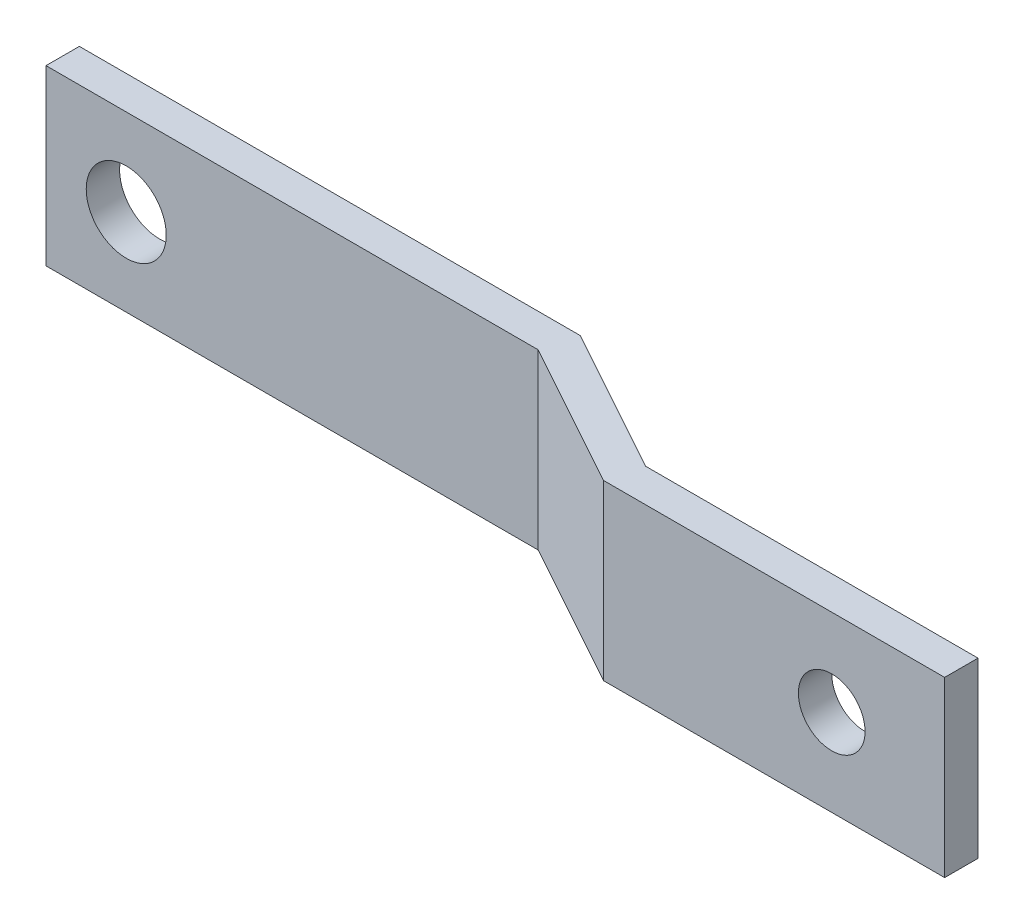
SolidWorks part; units mm, degrees
ref_plane "Front Plane" through (0, 0, 0) normal (0, 0, 1) x (1, 0, 0)
ref_plane "Top Plane" through (0, 0, 0) normal (0, 1, 0) x (1, 0, 0)
ref_plane "Right Plane" through (0, 0, 0) normal (1, 0, 0) x (0, 0, -1)
sketch "Sketch1" plane through (0, 0, 0) normal (0, 1, 0) x (1, 0, 0)
  line L0 (0, 0) -> (38.1391, 0)
  line L1 (38.1391, 0) -> (49.2453, -6.1289)
  line L2 (49.2453, -6.1289) -> (74.5674, -6.1289)
extrude "Extrude-Thin1" add sketch "Sketch1" along normal blind 13.208 thin
sketch "Sketch3" plane through (0, 0, 0) normal (0, 0, -1) x (-1, 0, 0)
  circle A0 centre (-6.1106, 6.604) radius 3.048
extrude "Cut-Extrude1" cut sketch "Sketch3" against normal up to next
sketch "Sketch4" plane through (0, 0, 8.6689) normal (0, 0, 1) x (1, 0, 0)
  line L0 (48.5909, 13.208) -> (74.5674, 13.208) construction
  circle A0 centre (65.9664, 6.604) radius 2.54
  point P4 (0, 0)
  point P5 (0, 0)
  point P8 (0, 0)
  dimension "D1" = 6.604
extrude "Cut-Extrude2" cut sketch "Sketch4" against normal up to next
